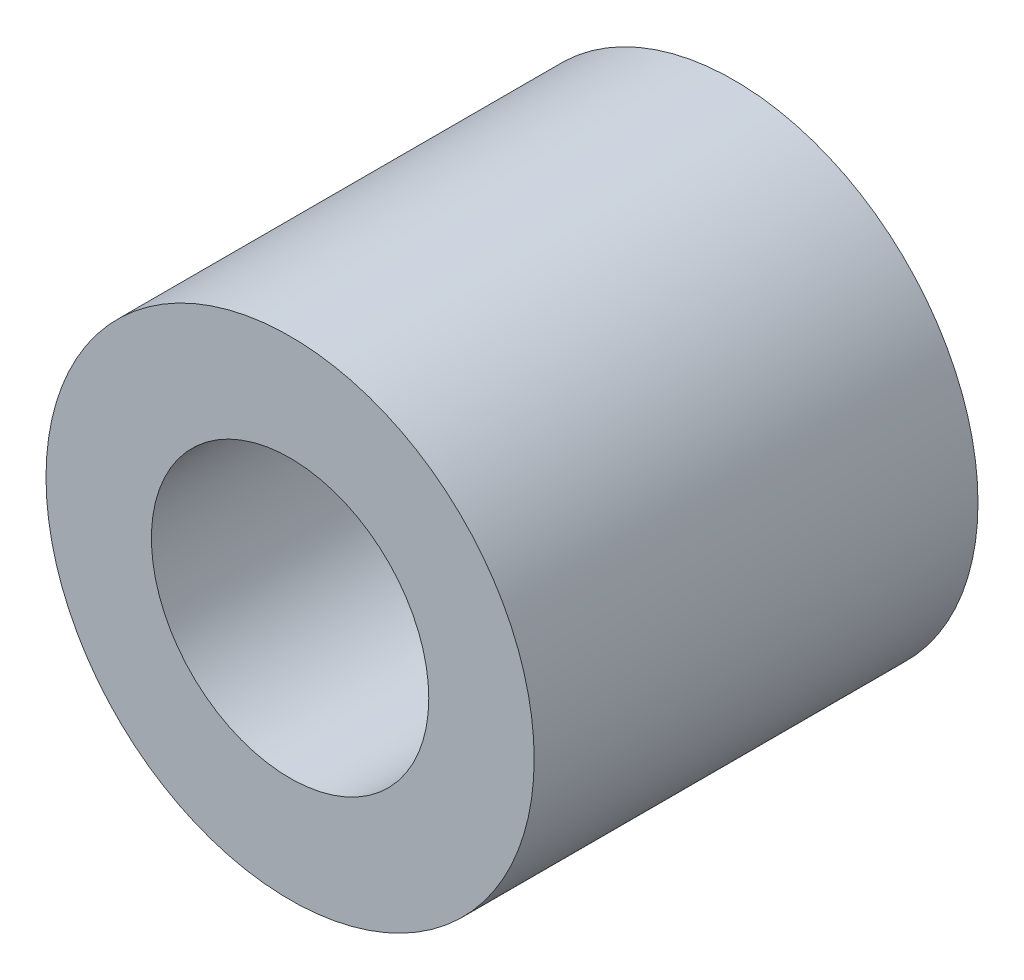
SolidWorks part; units mm, degrees
ref_plane "前视基准面" through (0, 0, 0) normal (0, 0, 1) x (1, 0, 0)
ref_plane "上视基准面" through (0, 0, 0) normal (0, 1, 0) x (1, 0, 0)
ref_plane "右视基准面" through (0, 0, 0) normal (1, 0, 0) x (0, 0, -1)
sketch "草图1" plane through (0, 0, 0) normal (0, 0, 1) x (1, 0, 0)
  circle A0 centre (0, 0) radius 1.25
  circle A1 centre (0, 0) radius 2.2
extrude "凸台-拉伸2" add sketch "草图1" along normal blind 4
